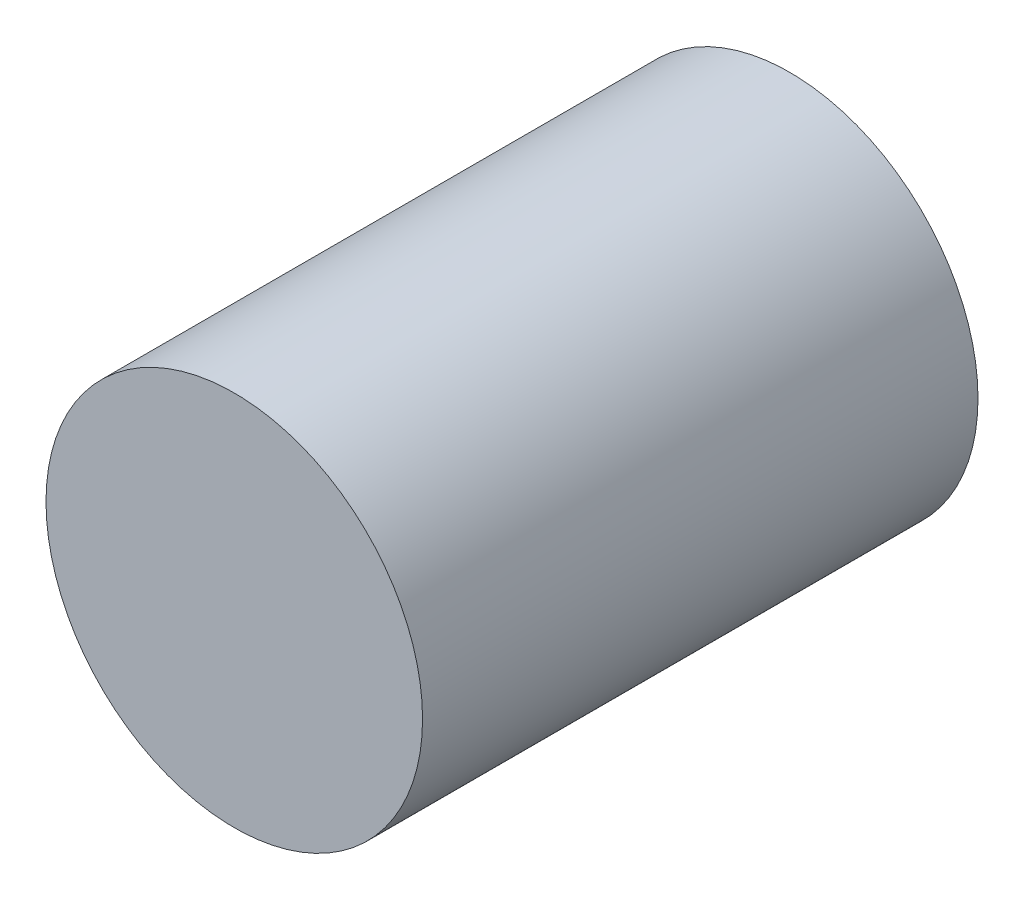
SolidWorks part; units mm, degrees
ref_plane "Front Plane" through (0, 0, 0) normal (0, 0, 1) x (1, 0, 0)
ref_plane "Top Plane" through (0, 0, 0) normal (0, 1, 0) x (1, 0, 0)
ref_plane "Right Plane" through (0, 0, 0) normal (1, 0, 0) x (0, 0, -1)
sketch "Sketch1" plane through (0, 0, 0) normal (0, 0, 1) x (1, 0, 0)
  circle A0 centre (0, 0) radius 30.5076
extrude "Boss-Extrude1" add sketch "Sketch1" along normal blind 90
